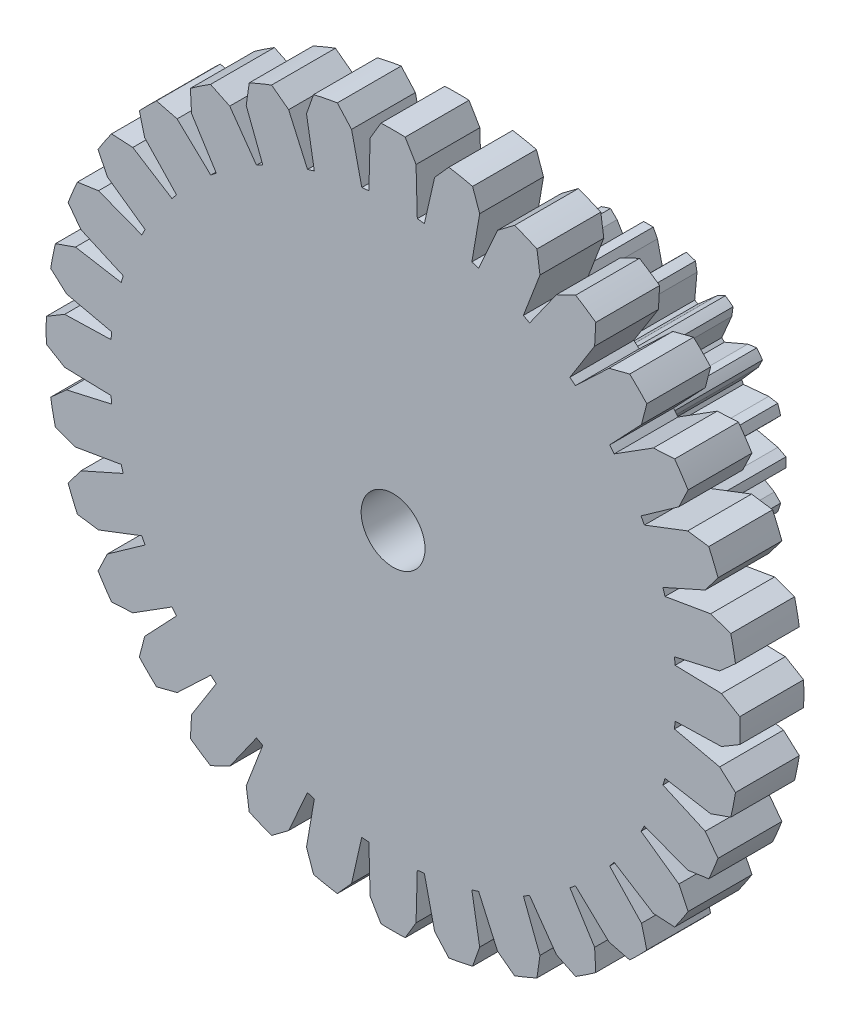
SolidWorks part; units mm, degrees
ref_plane "Front Plane" through (0, 0, 0) normal (0, 0, 1) x (1, 0, 0)
ref_plane "Top Plane" through (0, 0, 0) normal (0, 1, 0) x (1, 0, 0)
ref_plane "Right Plane" through (0, 0, 0) normal (1, 0, 0) x (0, 0, -1)
sketch "Sketch2" plane through (0, 0, 0) normal (0, 0, 1) x (1, 0, 0)
  line L0 (0, 0) -> (0, 5.435) construction
  line L2 (-0.3597, 5.1445) -> (-0.3791, 4.4188)
  line L3 (0.1897, 5.4317) -> (0.3597, 5.1445)
  line L4 (0.3597, 5.1445) -> (0.3791, 4.4188)
  line L5 (-0.1897, 5.4317) -> (-0.3597, 5.1445)
  line L6 (0.6508, 5.1159) -> (0.4902, 4.4078)
  line L7 (1.2457, 5.2903) -> (1.3565, 4.9755)
  line L8 (1.3565, 4.9755) -> (1.2339, 4.2599)
  line L9 (0.8736, 5.3643) -> (0.6508, 5.1159)
  line L10 (1.6364, 4.8906) -> (1.3407, 4.2275)
  line L11 (2.2539, 4.9456) -> (2.3011, 4.6153)
  line L12 (2.3011, 4.6153) -> (2.0413, 3.9373)
  line L13 (1.9034, 5.0908) -> (1.6364, 4.8906)
  line L14 (2.559, 4.4774) -> (2.1397, 3.8847)
  line L15 (3.1754, 4.4109) -> (3.1573, 4.0777)
  line L16 (3.1573, 4.0777) -> (2.7702, 3.4634)
  line L17 (2.86, 4.6217) -> (2.559, 4.4774)
  line L18 (3.3834, 3.8921) -> (2.8565, 3.3926)
  line L19 (3.9749, 3.7067) -> (3.8921, 3.3834)
  line L20 (3.8921, 3.3834) -> (3.3926, 2.8565)
  line L21 (3.7067, 3.9749) -> (3.3834, 3.8921)
  line L22 (4.0777, 3.1573) -> (3.4634, 2.7702)
  line L23 (4.6217, 2.86) -> (4.4774, 2.559)
  line L24 (4.4774, 2.559) -> (3.8847, 2.1397)
  line L25 (4.4109, 3.1754) -> (4.0777, 3.1573)
  line L26 (4.6153, 2.3011) -> (3.9373, 2.0413)
  line L27 (5.0908, 1.9034) -> (4.8906, 1.6364)
  line L28 (4.8906, 1.6364) -> (4.2275, 1.3407)
  line L29 (4.9456, 2.2539) -> (4.6153, 2.3011)
  line L30 (4.9755, 1.3565) -> (4.2599, 1.2339)
  line L31 (5.3643, 0.8736) -> (5.1159, 0.6508)
  line L32 (5.1159, 0.6508) -> (4.4078, 0.4902)
  line L33 (5.2903, 1.2457) -> (4.9755, 1.3565)
  line L34 (5.1445, 0.3597) -> (4.4188, 0.3791)
  line L35 (5.4317, -0.1897) -> (5.1445, -0.3597)
  line L36 (5.1445, -0.3597) -> (4.4188, -0.3791)
  line L37 (5.4317, 0.1897) -> (5.1445, 0.3597)
  line L38 (5.1159, -0.6508) -> (4.4078, -0.4902)
  line L39 (5.2903, -1.2457) -> (4.9755, -1.3565)
  line L40 (4.9755, -1.3565) -> (4.2599, -1.2339)
  line L41 (5.3643, -0.8736) -> (5.1159, -0.6508)
  line L42 (4.8906, -1.6364) -> (4.2275, -1.3407)
  line L43 (4.9456, -2.2539) -> (4.6153, -2.3011)
  line L44 (4.6153, -2.3011) -> (3.9373, -2.0413)
  line L45 (5.0908, -1.9034) -> (4.8906, -1.6364)
  line L46 (4.4774, -2.559) -> (3.8847, -2.1397)
  line L47 (4.4109, -3.1754) -> (4.0777, -3.1573)
  line L48 (4.0777, -3.1573) -> (3.4634, -2.7702)
  line L49 (4.6217, -2.86) -> (4.4774, -2.559)
  line L50 (3.8921, -3.3834) -> (3.3926, -2.8565)
  line L51 (3.7067, -3.9749) -> (3.3834, -3.8921)
  line L52 (3.3834, -3.8921) -> (2.8565, -3.3926)
  line L53 (3.9749, -3.7067) -> (3.8921, -3.3834)
  line L54 (3.1573, -4.0777) -> (2.7702, -3.4634)
  line L55 (2.86, -4.6217) -> (2.559, -4.4774)
  line L56 (2.559, -4.4774) -> (2.1397, -3.8847)
  line L57 (3.1754, -4.4109) -> (3.1573, -4.0777)
  line L58 (2.3011, -4.6153) -> (2.0413, -3.9373)
  line L59 (1.9034, -5.0908) -> (1.6364, -4.8906)
  line L60 (1.6364, -4.8906) -> (1.3407, -4.2275)
  line L61 (2.2539, -4.9456) -> (2.3011, -4.6153)
  line L62 (1.3565, -4.9755) -> (1.2339, -4.2599)
  line L63 (0.8736, -5.3643) -> (0.6508, -5.1159)
  line L64 (0.6508, -5.1159) -> (0.4902, -4.4078)
  line L65 (1.2457, -5.2903) -> (1.3565, -4.9755)
  line L66 (0.3597, -5.1445) -> (0.3791, -4.4188)
  line L67 (-0.1897, -5.4317) -> (-0.3597, -5.1445)
  line L68 (-0.3597, -5.1445) -> (-0.3791, -4.4188)
  line L69 (0.1897, -5.4317) -> (0.3597, -5.1445)
  line L70 (-0.6508, -5.1159) -> (-0.4902, -4.4078)
  line L71 (-1.2457, -5.2903) -> (-1.3565, -4.9755)
  line L72 (-1.3565, -4.9755) -> (-1.2339, -4.2599)
  line L73 (-0.8736, -5.3643) -> (-0.6508, -5.1159)
  line L74 (-1.6364, -4.8906) -> (-1.3407, -4.2275)
  line L75 (-2.2539, -4.9456) -> (-2.3011, -4.6153)
  line L76 (-2.3011, -4.6153) -> (-2.0413, -3.9373)
  line L77 (-1.9034, -5.0908) -> (-1.6364, -4.8906)
  line L78 (-2.559, -4.4774) -> (-2.1397, -3.8847)
  line L79 (-3.1754, -4.4109) -> (-3.1573, -4.0777)
  line L80 (-3.1573, -4.0777) -> (-2.7702, -3.4634)
  line L81 (-2.86, -4.6217) -> (-2.559, -4.4774)
  line L82 (-3.3834, -3.8921) -> (-2.8565, -3.3926)
  line L83 (-3.9749, -3.7067) -> (-3.8921, -3.3834)
  line L84 (-3.8921, -3.3834) -> (-3.3926, -2.8565)
  line L85 (-3.7067, -3.9749) -> (-3.3834, -3.8921)
  line L86 (-4.0777, -3.1573) -> (-3.4634, -2.7702)
  line L87 (-4.6217, -2.86) -> (-4.4774, -2.559)
  line L88 (-4.4774, -2.559) -> (-3.8847, -2.1397)
  line L89 (-4.4109, -3.1754) -> (-4.0777, -3.1573)
  line L90 (-4.6153, -2.3011) -> (-3.9373, -2.0413)
  line L91 (-5.0908, -1.9034) -> (-4.8906, -1.6364)
  line L92 (-4.8906, -1.6364) -> (-4.2275, -1.3407)
  line L93 (-4.9456, -2.2539) -> (-4.6153, -2.3011)
  line L94 (-4.9755, -1.3565) -> (-4.2599, -1.2339)
  line L95 (-5.3643, -0.8736) -> (-5.1159, -0.6508)
  line L96 (-5.1159, -0.6508) -> (-4.4078, -0.4902)
  line L97 (-5.2903, -1.2457) -> (-4.9755, -1.3565)
  line L98 (-5.1445, -0.3597) -> (-4.4188, -0.3791)
  line L99 (-5.4317, 0.1897) -> (-5.1445, 0.3597)
  line L100 (-5.1445, 0.3597) -> (-4.4188, 0.3791)
  line L101 (-5.4317, -0.1897) -> (-5.1445, -0.3597)
  line L102 (-5.1159, 0.6508) -> (-4.4078, 0.4902)
  line L103 (-5.2903, 1.2457) -> (-4.9755, 1.3565)
  line L104 (-4.9755, 1.3565) -> (-4.2599, 1.2339)
  line L105 (-5.3643, 0.8736) -> (-5.1159, 0.6508)
  line L106 (-4.8906, 1.6364) -> (-4.2275, 1.3407)
  line L107 (-4.9456, 2.2539) -> (-4.6153, 2.3011)
  line L108 (-4.6153, 2.3011) -> (-3.9373, 2.0413)
  line L109 (-5.0908, 1.9034) -> (-4.8906, 1.6364)
  line L110 (-4.4774, 2.559) -> (-3.8847, 2.1397)
  line L111 (-4.4109, 3.1754) -> (-4.0777, 3.1573)
  line L112 (-4.0777, 3.1573) -> (-3.4634, 2.7702)
  line L113 (-4.6217, 2.86) -> (-4.4774, 2.559)
  line L114 (-3.8921, 3.3834) -> (-3.3926, 2.8565)
  line L115 (-3.7067, 3.9749) -> (-3.3834, 3.8921)
  line L116 (-3.3834, 3.8921) -> (-2.8565, 3.3926)
  line L117 (-3.9749, 3.7067) -> (-3.8921, 3.3834)
  line L118 (-3.1573, 4.0777) -> (-2.7702, 3.4634)
  line L119 (-2.86, 4.6217) -> (-2.559, 4.4774)
  line L120 (-2.559, 4.4774) -> (-2.1397, 3.8847)
  line L121 (-3.1754, 4.4109) -> (-3.1573, 4.0777)
  line L122 (-2.3011, 4.6153) -> (-2.0413, 3.9373)
  line L123 (-1.9034, 5.0908) -> (-1.6364, 4.8906)
  line L124 (-1.6364, 4.8906) -> (-1.3407, 4.2275)
  line L125 (-2.2539, 4.9456) -> (-2.3011, 4.6153)
  line L126 (-1.3565, 4.9755) -> (-1.2339, 4.2599)
  line L127 (-0.8736, 5.3643) -> (-0.6508, 5.1159)
  line L128 (-0.6508, 5.1159) -> (-0.4902, 4.4078)
  line L129 (-1.2457, 5.2903) -> (-1.3565, 4.9755)
  arc A0 (0.1897, 5.4317) -> (-0.1897, 5.4317) centre (0, 0) ccw
  arc A1 (-1.2339, 4.2599) -> (-1.3407, 4.2275) centre (0, 0) ccw
  arc A2 (1.2457, 5.2903) -> (0.8736, 5.3643) centre (0, 0) ccw
  circle A3 centre (0, 0) radius 5.435 construction
  arc A4 (2.2539, 4.9456) -> (1.9034, 5.0908) centre (0, 0) ccw
  arc A5 (3.1754, 4.4109) -> (2.86, 4.6217) centre (0, 0) ccw
  arc A6 (3.9749, 3.7067) -> (3.7067, 3.9749) centre (0, 0) ccw
  arc A7 (4.6217, 2.86) -> (4.4109, 3.1754) centre (0, 0) ccw
  arc A8 (5.0908, 1.9034) -> (4.9456, 2.2539) centre (0, 0) ccw
  arc A9 (5.3643, 0.8736) -> (5.2903, 1.2457) centre (0, 0) ccw
  arc A10 (5.4317, -0.1897) -> (5.4317, 0.1897) centre (0, 0) ccw
  arc A11 (5.2903, -1.2457) -> (5.3643, -0.8736) centre (0, 0) ccw
  arc A12 (4.9456, -2.2539) -> (5.0908, -1.9034) centre (0, 0) ccw
  arc A13 (4.4109, -3.1754) -> (4.6217, -2.86) centre (0, 0) ccw
  arc A14 (3.7067, -3.9749) -> (3.9749, -3.7067) centre (0, 0) ccw
  arc A15 (2.86, -4.6217) -> (3.1754, -4.4109) centre (0, 0) ccw
  arc A16 (1.9034, -5.0908) -> (2.2539, -4.9456) centre (0, 0) ccw
  arc A17 (0.8736, -5.3643) -> (1.2457, -5.2903) centre (0, 0) ccw
  arc A18 (-0.1897, -5.4317) -> (0.1897, -5.4317) centre (0, 0) ccw
  arc A19 (-1.2457, -5.2903) -> (-0.8736, -5.3643) centre (0, 0) ccw
  arc A20 (-2.2539, -4.9456) -> (-1.9034, -5.0908) centre (0, 0) ccw
  arc A21 (-3.1754, -4.4109) -> (-2.86, -4.6217) centre (0, 0) ccw
  arc A22 (-3.9749, -3.7067) -> (-3.7067, -3.9749) centre (0, 0) ccw
  arc A23 (-4.6217, -2.86) -> (-4.4109, -3.1754) centre (0, 0) ccw
  arc A24 (-5.0908, -1.9034) -> (-4.9456, -2.2539) centre (0, 0) ccw
  arc A25 (-5.3643, -0.8736) -> (-5.2903, -1.2457) centre (0, 0) ccw
  arc A26 (-5.4317, 0.1897) -> (-5.4317, -0.1897) centre (0, 0) ccw
  arc A27 (-5.2903, 1.2457) -> (-5.3643, 0.8736) centre (0, 0) ccw
  arc A28 (-4.9456, 2.2539) -> (-5.0908, 1.9034) centre (0, 0) ccw
  arc A29 (-4.4109, 3.1754) -> (-4.6217, 2.86) centre (0, 0) ccw
  arc A30 (-3.7067, 3.9749) -> (-3.9749, 3.7067) centre (0, 0) ccw
  arc A31 (-2.86, 4.6217) -> (-3.1754, 4.4109) centre (0, 0) ccw
  arc A32 (-1.9034, 5.0908) -> (-2.2539, 4.9456) centre (0, 0) ccw
  arc A33 (-0.8736, 5.3643) -> (-1.2457, 5.2903) centre (0, 0) ccw
  arc A34 (-2.0413, 3.9373) -> (-2.1397, 3.8847) centre (0, 0) ccw
  circle A35 centre (0, 0) radius 4.435 construction
  arc A36 (-2.7702, 3.4634) -> (-2.8565, 3.3926) centre (0, 0) ccw
  arc A37 (-3.3926, 2.8565) -> (-3.4634, 2.7702) centre (0, 0) ccw
  arc A38 (-3.8847, 2.1397) -> (-3.9373, 2.0413) centre (0, 0) ccw
  arc A39 (-4.2275, 1.3407) -> (-4.2599, 1.2339) centre (0, 0) ccw
  arc A40 (-4.4078, 0.4902) -> (-4.4188, 0.3791) centre (0, 0) ccw
  arc A41 (-4.4188, -0.3791) -> (-4.4078, -0.4902) centre (0, 0) ccw
  arc A42 (-4.2599, -1.2339) -> (-4.2275, -1.3407) centre (0, 0) ccw
  arc A43 (-3.9373, -2.0413) -> (-3.8847, -2.1397) centre (0, 0) ccw
  arc A44 (-3.4634, -2.7702) -> (-3.3926, -2.8565) centre (0, 0) ccw
  arc A45 (-2.8565, -3.3926) -> (-2.7702, -3.4634) centre (0, 0) ccw
  arc A46 (-2.1397, -3.8847) -> (-2.0413, -3.9373) centre (0, 0) ccw
  arc A47 (-1.3407, -4.2275) -> (-1.2339, -4.2599) centre (0, 0) ccw
  arc A48 (-0.4902, -4.4078) -> (-0.3791, -4.4188) centre (0, 0) ccw
  arc A49 (0.3791, -4.4188) -> (0.4902, -4.4078) centre (0, 0) ccw
  arc A50 (1.2339, -4.2599) -> (1.3407, -4.2275) centre (0, 0) ccw
  arc A51 (2.0413, -3.9373) -> (2.1397, -3.8847) centre (0, 0) ccw
  arc A52 (2.7702, -3.4634) -> (2.8565, -3.3926) centre (0, 0) ccw
  arc A53 (3.3926, -2.8565) -> (3.4634, -2.7702) centre (0, 0) ccw
  arc A54 (3.8847, -2.1397) -> (3.9373, -2.0413) centre (0, 0) ccw
  arc A55 (4.2275, -1.3407) -> (4.2599, -1.2339) centre (0, 0) ccw
  arc A56 (4.4078, -0.4902) -> (4.4188, -0.3791) centre (0, 0) ccw
  arc A57 (4.4188, 0.3791) -> (4.4078, 0.4902) centre (0, 0) ccw
  arc A58 (4.2599, 1.2339) -> (4.2275, 1.3407) centre (0, 0) ccw
  arc A59 (3.9373, 2.0413) -> (3.8847, 2.1397) centre (0, 0) ccw
  arc A60 (3.4634, 2.7702) -> (3.3926, 2.8565) centre (0, 0) ccw
  arc A61 (2.8565, 3.3926) -> (2.7702, 3.4634) centre (0, 0) ccw
  arc A62 (2.1397, 3.8847) -> (2.0413, 3.9373) centre (0, 0) ccw
  arc A63 (1.3407, 4.2275) -> (1.2339, 4.2599) centre (0, 0) ccw
  arc A64 (0.4902, 4.4078) -> (0.3791, 4.4188) centre (0, 0) ccw
  arc A65 (-0.3791, 4.4188) -> (-0.4902, 4.4078) centre (0, 0) ccw
  point P7 (5.1975, 1.589)
  point P13 (4.435, 0)
  point P201 (0, 0)
  dimension "D1" = 10.87
  dimension "D3" = 32
  dimension "D2" = 1
extrude "Boss-Extrude1" add sketch "Sketch2" along normal blind 1
sketch "Sketch3" plane through (0, 0, 1) normal (0, 0, 1) x (1, 0, 0)
  circle A0 centre (0, 0) radius 0.5
extrude "Cut-Extrude1" cut sketch "Sketch3" against normal blind 1
sketch "Sketch4" plane through (0, 0, 0) normal (0, 0, -1) x (-1, 0, 0)
  line L0 (0, 0) -> (0, 2.155) construction
  line L1 (0, 0) -> (0.2303, 1.6389) construction
  line L2 (0.7371, 2.025) -> (0.7612, 1.884)
  line L3 (0.0752, 2.1537) -> (0.1417, 2.027)
  line L4 (0.1417, 2.027) -> (0.2303, 1.6389)
  line L5 (-0.0752, 2.1537) -> (-0.1417, 2.027)
  line L6 (-0.1417, 2.027) -> (-0.2303, 1.6389)
  line L7 (0.7612, 1.884) -> (0.7255, 1.4875)
  line L8 (0.594, 2.0715) -> (0.4916, 1.9716)
  line L9 (0.4916, 1.9716) -> (0.2874, 1.6299)
  line L10 (1.3268, 1.6982) -> (1.3061, 1.5565)
  line L11 (1.3061, 1.5565) -> (1.1497, 1.1905)
  line L12 (1.2051, 1.7866) -> (1.0767, 1.7232)
  line L13 (1.0767, 1.7232) -> (0.777, 1.4613)
  line L14 (1.7866, 1.2051) -> (1.7232, 1.0767)
  line L15 (1.7232, 1.0767) -> (1.4613, 0.777)
  line L16 (1.6982, 1.3268) -> (1.5565, 1.3061)
  line L17 (1.5565, 1.3061) -> (1.1905, 1.1497)
  line L18 (2.0715, 0.594) -> (1.9716, 0.4916)
  line L19 (1.9716, 0.4916) -> (1.6299, 0.2874)
  line L20 (2.025, 0.7371) -> (1.884, 0.7612)
  line L21 (1.884, 0.7612) -> (1.4875, 0.7255)
  line L22 (2.1537, -0.0752) -> (2.027, -0.1417)
  line L23 (2.027, -0.1417) -> (1.6389, -0.2303)
  line L24 (2.1537, 0.0752) -> (2.027, 0.1417)
  line L25 (2.027, 0.1417) -> (1.6389, 0.2303)
  line L26 (2.025, -0.7371) -> (1.884, -0.7612)
  line L27 (1.884, -0.7612) -> (1.4875, -0.7255)
  line L28 (2.0715, -0.594) -> (1.9716, -0.4916)
  line L29 (1.9716, -0.4916) -> (1.6299, -0.2874)
  line L30 (1.6982, -1.3268) -> (1.5565, -1.3061)
  line L31 (1.5565, -1.3061) -> (1.1905, -1.1497)
  line L32 (1.7866, -1.2051) -> (1.7232, -1.0767)
  line L33 (1.7232, -1.0767) -> (1.4613, -0.777)
  line L34 (1.2051, -1.7866) -> (1.0767, -1.7232)
  line L35 (1.0767, -1.7232) -> (0.777, -1.4613)
  line L36 (1.3268, -1.6982) -> (1.3061, -1.5565)
  line L37 (1.3061, -1.5565) -> (1.1497, -1.1905)
  line L38 (0.594, -2.0715) -> (0.4916, -1.9716)
  line L39 (0.4916, -1.9716) -> (0.2874, -1.6299)
  line L40 (0.7371, -2.025) -> (0.7612, -1.884)
  line L41 (0.7612, -1.884) -> (0.7255, -1.4875)
  line L42 (-0.0752, -2.1537) -> (-0.1417, -2.027)
  line L43 (-0.1417, -2.027) -> (-0.2303, -1.6389)
  line L44 (0.0752, -2.1537) -> (0.1417, -2.027)
  line L45 (0.1417, -2.027) -> (0.2303, -1.6389)
  line L46 (-0.7371, -2.025) -> (-0.7612, -1.884)
  line L47 (-0.7612, -1.884) -> (-0.7255, -1.4875)
  line L48 (-0.594, -2.0715) -> (-0.4916, -1.9716)
  line L49 (-0.4916, -1.9716) -> (-0.2874, -1.6299)
  line L50 (-1.3268, -1.6982) -> (-1.3061, -1.5565)
  line L51 (-1.3061, -1.5565) -> (-1.1497, -1.1905)
  line L52 (-1.2051, -1.7866) -> (-1.0767, -1.7232)
  line L53 (-1.0767, -1.7232) -> (-0.777, -1.4613)
  line L54 (-1.7866, -1.2051) -> (-1.7232, -1.0767)
  line L55 (-1.7232, -1.0767) -> (-1.4613, -0.777)
  line L56 (-1.6982, -1.3268) -> (-1.5565, -1.3061)
  line L57 (-1.5565, -1.3061) -> (-1.1905, -1.1497)
  line L58 (-2.0715, -0.594) -> (-1.9716, -0.4916)
  line L59 (-1.9716, -0.4916) -> (-1.6299, -0.2874)
  line L60 (-2.025, -0.7371) -> (-1.884, -0.7612)
  line L61 (-1.884, -0.7612) -> (-1.4875, -0.7255)
  line L62 (-2.1537, 0.0752) -> (-2.027, 0.1417)
  line L63 (-2.027, 0.1417) -> (-1.6389, 0.2303)
  line L64 (-2.1537, -0.0752) -> (-2.027, -0.1417)
  line L65 (-2.027, -0.1417) -> (-1.6389, -0.2303)
  line L66 (-2.025, 0.7371) -> (-1.884, 0.7612)
  line L67 (-1.884, 0.7612) -> (-1.4875, 0.7255)
  line L68 (-2.0715, 0.594) -> (-1.9716, 0.4916)
  line L69 (-1.9716, 0.4916) -> (-1.6299, 0.2874)
  line L70 (-1.6982, 1.3268) -> (-1.5565, 1.3061)
  line L71 (-1.5565, 1.3061) -> (-1.1905, 1.1497)
  line L72 (-1.7866, 1.2051) -> (-1.7232, 1.0767)
  line L73 (-1.7232, 1.0767) -> (-1.4613, 0.777)
  line L74 (-1.2051, 1.7866) -> (-1.0767, 1.7232)
  line L75 (-1.0767, 1.7232) -> (-0.777, 1.4613)
  line L76 (-1.3268, 1.6982) -> (-1.3061, 1.5565)
  line L77 (-1.3061, 1.5565) -> (-1.1497, 1.1905)
  line L78 (-0.594, 2.0715) -> (-0.4916, 1.9716)
  line L79 (-0.4916, 1.9716) -> (-0.2874, 1.6299)
  line L80 (-0.7371, 2.025) -> (-0.7612, 1.884)
  line L81 (-0.7612, 1.884) -> (-0.7255, 1.4875)
  arc A0 (0.2874, 1.6299) -> (0.2303, 1.6389) centre (0, 0) ccw
  arc A1 (0.0752, 2.1537) -> (-0.0752, 2.1537) centre (0, 0) ccw
  arc A2 (0.7371, 2.025) -> (0.594, 2.0715) centre (0, 0) ccw
  circle A3 centre (0, 0) radius 2.155 construction
  arc A4 (1.3268, 1.6982) -> (1.2051, 1.7866) centre (0, 0) ccw
  arc A5 (1.7866, 1.2051) -> (1.6982, 1.3268) centre (0, 0) ccw
  arc A6 (2.0715, 0.594) -> (2.025, 0.7371) centre (0, 0) ccw
  arc A7 (2.1537, -0.0752) -> (2.1537, 0.0752) centre (0, 0) ccw
  arc A8 (2.025, -0.7371) -> (2.0715, -0.594) centre (0, 0) ccw
  arc A9 (1.6982, -1.3268) -> (1.7866, -1.2051) centre (0, 0) ccw
  arc A10 (1.2051, -1.7866) -> (1.3268, -1.6982) centre (0, 0) ccw
  arc A11 (0.594, -2.0715) -> (0.7371, -2.025) centre (0, 0) ccw
  arc A12 (-0.0752, -2.1537) -> (0.0752, -2.1537) centre (0, 0) ccw
  arc A13 (-0.7371, -2.025) -> (-0.594, -2.0715) centre (0, 0) ccw
  arc A14 (-1.3268, -1.6982) -> (-1.2051, -1.7866) centre (0, 0) ccw
  arc A15 (-1.7866, -1.2051) -> (-1.6982, -1.3268) centre (0, 0) ccw
  arc A16 (-2.0715, -0.594) -> (-2.025, -0.7371) centre (0, 0) ccw
  arc A17 (-2.1537, 0.0752) -> (-2.1537, -0.0752) centre (0, 0) ccw
  arc A18 (-2.025, 0.7371) -> (-2.0715, 0.594) centre (0, 0) ccw
  arc A19 (-1.6982, 1.3268) -> (-1.7866, 1.2051) centre (0, 0) ccw
  arc A20 (-1.2051, 1.7866) -> (-1.3268, 1.6982) centre (0, 0) ccw
  arc A21 (-0.594, 2.0715) -> (-0.7371, 2.025) centre (0, 0) ccw
  arc A22 (0.777, 1.4613) -> (0.7255, 1.4875) centre (0, 0) ccw
  circle A23 centre (0, 0) radius 1.655 construction
  arc A24 (1.1905, 1.1497) -> (1.1497, 1.1905) centre (0, 0) ccw
  arc A25 (1.4875, 0.7255) -> (1.4613, 0.777) centre (0, 0) ccw
  arc A26 (1.6389, 0.2303) -> (1.6299, 0.2874) centre (0, 0) ccw
  arc A27 (1.6299, -0.2874) -> (1.6389, -0.2303) centre (0, 0) ccw
  arc A28 (1.4613, -0.777) -> (1.4875, -0.7255) centre (0, 0) ccw
  arc A29 (1.1497, -1.1905) -> (1.1905, -1.1497) centre (0, 0) ccw
  arc A30 (0.7255, -1.4875) -> (0.777, -1.4613) centre (0, 0) ccw
  arc A31 (0.2303, -1.6389) -> (0.2874, -1.6299) centre (0, 0) ccw
  arc A32 (-0.2874, -1.6299) -> (-0.2303, -1.6389) centre (0, 0) ccw
  arc A33 (-1.1905, -1.1497) -> (-0.7255, -1.4875) centre (0, 0) ccw
  arc A34 (-1.4875, -0.7255) -> (-1.4613, -0.777) centre (0, 0) ccw
  arc A35 (-1.6389, -0.2303) -> (-1.6299, -0.2874) centre (0, 0) ccw
  arc A36 (-1.6299, 0.2874) -> (-1.6389, 0.2303) centre (0, 0) ccw
  arc A37 (-1.4613, 0.777) -> (-1.4875, 0.7255) centre (0, 0) ccw
  arc A38 (-1.1497, 1.1905) -> (-1.1905, 1.1497) centre (0, 0) ccw
  arc A39 (-0.7255, 1.4875) -> (-0.777, 1.4613) centre (0, 0) ccw
  arc A40 (-0.2303, 1.6389) -> (-0.2874, 1.6299) centre (0, 0) ccw
  circle A41 centre (0, 0) radius 0.5 construction
  circle A42 centre (0, 0) radius 0.5
  point P5 (2.155, 0)
  point P9 (1.5827, 0.4839)
  point P130 (0, 0)
  dimension "D1" = 3.31
  dimension "D3" = 8
  dimension "D2" = 0.5
  dimension "D4" = 20
extrude "Boss-Extrude2" add sketch "Sketch4" along normal blind 3 contours L6 A40 L79 L78 A21 L80 L81 A39 L75 L74 A20 L76 L77 A38 L71 L70 A19 L72 L73 A37 L67 L66 A18 L68 L69 A36 L63 L62 A17 L64 L65 A35 L59 L58 A16 L60 L61 A34 L55 L54 A15 L56 L57 A33 L47 L46 A13 L48 L49
